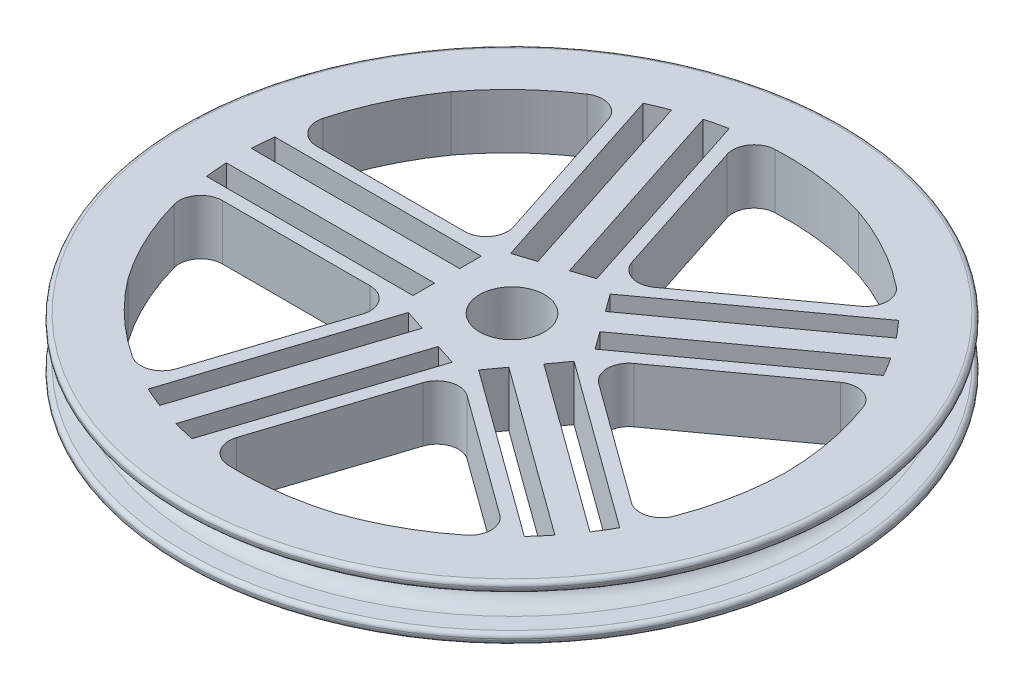
SolidWorks part; units mm, degrees
material "6061 Alloy"
ref_plane "Front Plane" through (0, 0, 0) normal (0, 0, 1) x (1, 0, 0)
ref_plane "Top Plane" through (0, 0, 0) normal (0, 1, 0) x (1, 0, 0)
ref_plane "Right Plane" through (0, 0, 0) normal (1, 0, 0) x (0, 0, -1)
sketch "Sketch1" plane through (0, 0, 0) normal (0, 0, 1) x (1, 0, 0)
  line L3 (0, 8) -> (-4, 8)
  line L4 (0, 0) -> (-4, 0)
  line L5 (-5, 9) -> (-5, 9.35)
  line L6 (-4, 10.35) -> (71.2, 10.35)
  line L7 (0, 4) -> (7.1457, 4) construction
  line L8 (-5, -1) -> (-5, -1.35)
  line L9 (-4, -2.35) -> (71.2, -2.35)
  line L10 (71.2, 10.35) -> (71.2, -2.35)
  arc A1 (0, 8) -> (0, 0) centre (0, 4) cw
  arc A2 (-4, 8) -> (-5, 9) centre (-4, 9) cw
  arc A3 (-4, 0) -> (-5, -1) centre (-4, -1) ccw
  arc A4 (-5, 9.35) -> (-4, 10.35) centre (-4, 9.35) cw
  arc A5 (-5, -1.35) -> (-4, -2.35) centre (-4, -1.35) ccw
  point P14 (-5, 8)
  point P17 (-5, 0)
  point P20 (-5, 10.35)
  point P23 (-5, -2.35)
  dimension "D2" = 4
  dimension "D7" = 1
  dimension "D8" = 1
  dimension "D1" = 8
  dimension "D3" = 5
  dimension "D4" = 5
  dimension "D5" = 76.2
  dimension "D6" = 2.35
revolve "Revolve2" add sketch "Sketch1" angle 360 about L10
sketch "Sketch2" plane through (0, -2.35, 0) normal (0, -1, 0) x (1, 0, 0)
  line L5 (71.2, 0) -> (128.6984, 0) construction
  circle A0 centre (71.2, 0) radius 7.5
  dimension "D1" = 15
extrude "Cut-Extrude3" cut sketch "Sketch2" against normal through all
sketch "Sketch3" plane through (0, -2.35, 0) normal (0, -1, 0) x (1, 0, 0)
  line L0 (71.2, 0) -> (130.5671, 0) construction
  line L2 (89.741, 0) -> (76.9295, 17.6336)
  line L3 (76.9295, 17.6336) -> (56.2, 10.8981)
  line L4 (56.2, 10.8981) -> (56.2, -10.8981)
  line L5 (56.2, -10.8981) -> (76.9295, -17.6336)
  line L6 (76.9295, -17.6336) -> (89.741, 0)
  line L7 (71.2, 0) -> (76.9295, 17.6336)
  line L8 (76.9295, 17.6336) -> (90.8353, 60.4311)
  line L9 (71.2, 0) -> (89.741, 0)
  line L10 (89.741, 0) -> (134.741, 0)
  line L11 (81.6318, 11.1614) -> (120.5799, 39.4589)
  line L12 (85.0387, 6.4721) -> (123.9869, 34.7696)
  line L13 (76.9295, 17.6336) -> (115.1855, 45.4282)
  line L14 (78.6928, 15.2065) -> (117.3036, 43.2589)
  line L15 (89.741, 0) -> (127.997, 27.7946)
  line L16 (87.9777, 2.4271) -> (126.5884, 30.4794)
  circle A1 centre (71.2, 0) radius 15 construction
  arc A2 (90.8353, 60.4311) -> (134.741, 0) centre (69.7496, -1.0538) cw
  dimension "D5" = 90
  dimension "D6" = 90
  dimension "D7" = 8
  dimension "D1" = 30
  dimension "D4" = 65
  dimension "D2" = 45
  dimension "D3" = 45
  dimension "D8" = 8
  dimension "D9" = 3
  dimension "D10" = 90
  dimension "D11" = 3
sketch "Sketch5" plane through (0, -2.35, 0) normal (0, -1, 0) x (1, 0, 0)
  line L0 (71.2, 0) -> (71.2, 9.89)
  line L1 (68.81, 9.89) -> (73.59, 9.89)
  line L4 (71.2, 9.89) -> (71.2, 7.5)
  line L5 (68.81, 9.89) -> (68.81, 5.1275)
  line L6 (73.59, 9.89) -> (73.59, 5.1275)
  line L7 (68.81, 5.1275) -> (73.59, 5.1275)
  circle A1 centre (71.2, 0) radius 7.5 construction
  circle M28 centre (71.2, 0) radius 7.5
  dimension "D2" = 2.39
  dimension "D1" = 2.39
  dimension "D3" = 4.7625
extrude "Cut-Extrude7" cut sketch "Sketch3" against normal through all both and the other way through all contours A2 L8 L13 | A2 L14 L2 L11 | A2 L12 L2 L16 | A2 L15 L10
pattern_circular "CirPattern1" count 5 over 360 about axis through (71.2, 0, 0) along (0, 1, 0) of "Cut-Extrude7"
fillet "Fillet1" radius 5 5 edges at (76.9295, 4, -17.6336) (89.741, 4, 0) (76.9295, 4, 17.6336) (56.2, 4, 10.8981) (56.2, 4, -10.8981)
fillet "Fillet2" radius 5 10 edges at (115.1855, 4, 45.4282) (127.997, 4, 27.7946) (127.997, 4, -27.7946) (115.1855, 4, -45.4282) (41.5875, 4, -55.8708) (62.317, 4, -62.6062) (8.913, 4, -10.8981) (8.913, 4, 10.8981) (41.5875, 4, 55.8708) (62.317, 4, 62.6062)
sketch "Sketch6" plane through (0, -2.35, 0) normal (0, -1, 0) x (1, 0, 0)
  line L1 (76.9785, 36.1222) -> (102.3785, 36.1222)
  line L2 (76.9785, 36.1222) -> (76.9785, 61.5222)
  line L3 (76.9785, 61.5222) -> (102.3785, 61.5222)
  line L4 (102.3785, 36.1222) -> (102.3785, 61.5222)
  dimension "D1" = 25.4
  dimension "D2" = 25.4
extrude "Boss-Extrude1" add sketch "Sketch5" against normal blind 10 contours L1 L5 L0 M28 | L6 L1 L0 M28 | L0 L7 L6 M28 | L5 L7 L0 M28
sketch "Sketch7" plane through (0, -2.35, 0) normal (0, -1, 0) x (1, 0, 0)
  line L1 (133.6884, 74.8316) -> (159.0884, 74.8316)
  line L2 (133.6884, 74.8316) -> (133.6884, 49.4316)
  line L3 (133.6884, 49.4316) -> (159.0884, 49.4316)
  line L4 (159.0884, 74.8316) -> (159.0884, 49.4316)
  dimension "D1" = 25.4
  dimension "D2" = 25.4
